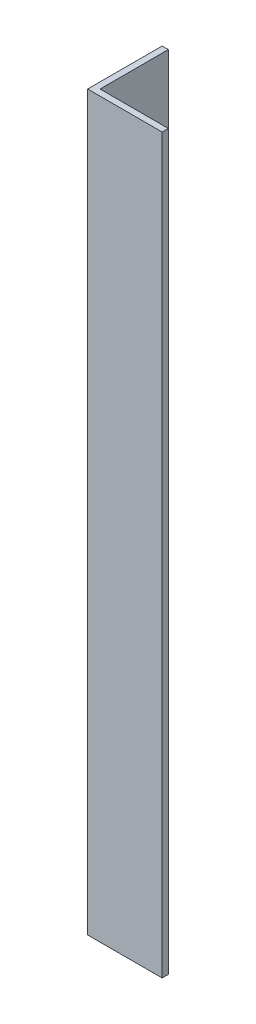
SolidWorks part; units mm, degrees
ref_plane "Front" through (0, 0, 0) normal (0, 0, 1) x (1, 0, 0)
ref_plane "Top" through (0, 0, 0) normal (0, 1, 0) x (1, 0, 0)
ref_plane "Right" through (0, 0, 0) normal (1, 0, 0) x (0, 0, -1)
sketch "Sketch1" plane through (0, 0, 0) normal (0, 1, 0) x (1, 0, 0)
  line L0 (0, 0) -> (19.05, 0)
  line L1 (0, 0) -> (0, 19.05)
  line L2 (1.5875, 1.5875) -> (1.5875, 19.05)
  line L3 (1.5875, 1.5875) -> (19.05, 1.5875)
  line L4 (0, 19.05) -> (1.5875, 19.05)
  line L5 (19.05, 1.5875) -> (19.05, 0)
extrude "Boss-Extrude1" add sketch "Sketch1" along normal blind 187.325
